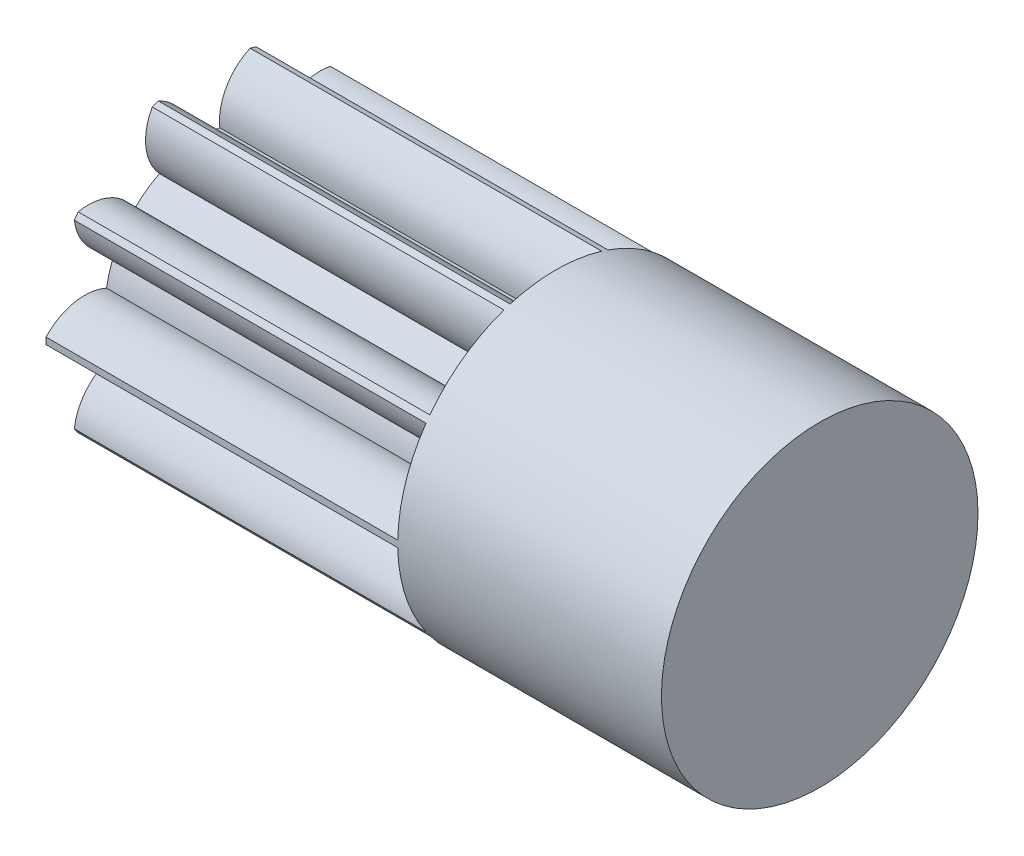
SolidWorks part; units mm, degrees
ref_plane "Plane1" through (0, 0, 0) normal (0, 0, 1) x (1, 0, 0)
ref_plane "Plane2" through (0, 0, 0) normal (0, 1, 0) x (1, 0, 0)
ref_plane "Plane3" through (0, 0, 0) normal (1, 0, 0) x (0, 0, -1)
sketch "HoldingSke" plane through (0, 0, 0) normal (0, 1, 0) x (1, 0, 0)
  line L0 (0, 0) -> (0.6565, -0.1158)
  line L1 (-15, 0) -> (100, 0) construction
  line L2 (0, 0) -> (-2.1039, 2.3779)
  line L3 (0, 0) -> (-11.863, 4.5341)
  line L4 (0, 0) -> (8.5048, 1.4996)
  line L5 (0, 0) -> (-46.8476, -17.4728)
  line L6 (0, 0) -> (-16.5793, -11.1861)
  line L7 (-2.1039, 2.3779) -> (8.6586, 51.2059)
  line L8 (-76.2, 54.61) -> (-75.3, 54.61)
  line L9 (-71.009, 38.7566) -> (-53.1078, 45.2721)
  line L10 (-76.2, 71.12) -> (104.1128, 71.12)
  line L11 (0, 0) -> (-20, 0)
  line L12 (-76.2, 101.6) -> (-76.147, 101.6)
  line L13 (24.9733, 27.94) -> (52.9518, 28.4284)
  line L14 (24.9733, 27.94) -> (24.9743, 27.94)
  line L15 (24.9733, 27.94) -> (100.4006, 29.5858)
  line L16 (-63.627, -1.5) -> (-12.827, -1.5)
  circle A0 centre (0, 0) radius 2.5
  circle A1 centre (0, 0) radius 5.624
  circle A2 centre (0, 0) radius 37.5
  circle A3 centre (0, 0) radius 2.5
  dimension "MHD" = 11.248
  dimension "Hub_dia" = 75
  dimension "Bore" = 5
  dimension "MBD" = 5
  dimension "Num_teeth" = 10
  dimension "Pitch" = 0.6667
  dimension "Overall_len" = 50
  dimension "Show_teeth" = 10
  dimension "Thickness" = 20
  dimension "OAL" = 50.0001
  dimension "T_dim" = 0.9
  dimension "Ap" = 20
  dimension "H" = 19.05
  dimension "Pitch_radius" = 180.3128
  dimension "Width" = 20
  dimension "Backlash" = 0.053
  dimension "Addendum_fac" = 1
  dimension "Dedendum_fac" = 1.25
  dimension "Clearance_fac" = 0.25
  dimension "Dedendum_add" = 0.001
  dimension "Module" = 1.5
sketch "BasProSke" plane through (0, 0, 0) normal (0, 1, 0) x (1, 0, 0)
  line L0 (-10, 0) -> (60, 0) construction
  line L1 (0, 0) -> (0, 9)
  line L2 (0, 0) -> (20, 0)
  line L3 (20, 0) -> (20, 9)
  line L4 (20, 9) -> (0, 9)
  dimension "Thickness" = 20
  dimension "Diameter" = 18
revolve "Base-Revolve" add sketch "BasProSke" angle 360 about L0
sketch "TooCutSke" plane through (0, 0, 0) normal (1, 0, 0) x (0, 0, -1)
  line L1 (0, 0) -> (0, 107) construction
  line L2 (0, 0) -> (-1.2658, 7.3924) construction
  line L3 (0, 0) -> (-4.5869, 14.117) construction
  line L4 (-1.2658, 7.3924) -> (-2.2934, 7.0585) construction
  arc A0 (0.8839, 5.5541) -> (-0.8839, 5.5541) centre (0, 0) ccw
  arc A1 (2.6378, 8.6313) -> (-2.6378, 8.6313) centre (0, 0) ccw
  circle A2 centre (0, 0) radius 7.5 construction
  circle A3 centre (0, 0) radius 7.0477 construction
  arc A4 (-0.8839, 5.5541) -> (-2.6378, 8.6313) centre (-3.8646, 5.8936) ccw
  arc A5 (2.6378, 8.6313) -> (0.8839, 5.5541) centre (3.8646, 5.8936) ccw
  dimension "Root_dia" = 11.248
  dimension "Overcut_dia" = 18.0508
  dimension "Pitch_dia" = 15
  dimension "Base_dia" = 14.0954
  dimension "Flank_rad" = 3
  dimension "Half_ang" = 18
  dimension "Half_CT" = 1.0805
extrude "ToothCut" cut sketch "TooCutSke" along normal through all
fillet "Breaks" [suppressed] radius 0.03
fillet "RootFillets" [suppressed] radius 0.376
pattern_circular "TeethCuts" count 10 every 36 about axis through (-10, 0, 0) along (1, 0, 0) of "ToothCut", "RootFillets", "Breaks"
sketch "HubNeaOneSke" plane through (0, 0, 0) normal (-1, 0, 0) x (0, 0, 1)
  circle A0 centre (0, 0) radius 5.624
  dimension "Diameter" = 11.248
extrude "HubNearOne" [suppressed] add sketch "HubNeaOneSke" along normal blind 30.0001
sketch "HubNeaBotSke" plane through (0, 0, 0) normal (-1, 0, 0) x (0, 0, 1)
  circle A0 centre (0, 0) radius 5.624
  dimension "Diameter" = 11.248
extrude "HubNearBoth" [suppressed] add sketch "HubNeaBotSke" along normal blind 15
ref_plane "FarPln" through (20, 0, 0) normal (1, 0, 0) x (0, 0, -1)
sketch "HubFarSke" plane through (20, 0, 0) normal (1, 0, 0) x (0, 0, -1)
  circle A0 centre (0, 0) radius 5.624
  dimension "Diameter" = 11.248
extrude "HubFar" [suppressed] add sketch "HubFarSke" along normal blind 15
sketch "BorSke" plane through (0, 0, 0) normal (1, 0, 0) x (0, 0, -1)
  circle A0 centre (0, 0) radius 2.5
  dimension "Diameter" = 5
extrude "Bore" cut sketch "BorSke" along normal mid plane 100.0001
sketch "KeySke" plane through (0, 0, 0) normal (1, 0, 0) x (0, 0, -1)
  line L0 (-1, 0) -> (-1, 3.4)
  line L1 (-1, 3.4) -> (1, 3.4)
  line L2 (1, 3.4) -> (1, 0)
  line L3 (0, 0) -> (0, 34) construction
  line L4 (-1, 0) -> (1, 0)
  dimension "Offset" = 3.4
extrude "Keyway" [suppressed] cut sketch "KeySke" along normal mid plane 100.0001
pattern_circular "Keyway2" [suppressed] count 2 every 90 about axis through (-10, 0, 0) along (1, 0, 0)
sketch "Çizim1" plane through (20, 0, 0) normal (1, 0, 0) x (0, 0, -1)
  circle A1 centre (0, 0) radius 3
  dimension "D1" = 6
extrude "Yükseklik-Ekstrüzyon3" add sketch "Çizim1" against normal blind 20
sketch "Çizim2" plane through (20, 0, 0) normal (1, 0, 0) x (0, 0, -1)
  circle A0 centre (0, 0) radius 9
extrude "Yükseklik-Ekstrüzyon4" add sketch "Çizim2" along normal blind 15
equation "' \"Module@HoldingSke\" = 6.35"
equation "' \"Num_teeth@HoldingSke\" = 12"
equation "' \"Ap@HoldingSke\" =  20"
equation "' \"Ap@HoldingSke\" = 20"
equation "' \"Width@HoldingSke\" = 0.5 * 25.4"
equation "' \"Hub_dia@HoldingSke\"= 1 * 25.4"
equation "' \"Hub_dia@HoldingSke\" = 1 * 25.4"
equation "' \"Overall_len@HoldingSke\" = 1.0 * 25.4"
equation "' \"Bore@HoldingSke\" = 0.75 * 25.4"
equation "' \"T_dim@HoldingSke\" = 0.1 * 25.4"
equation "' \"Width@KeySke\" = 0.25 * 25.4"
equation "' \"Show_teeth@HoldingSke\" = 13"
equation "' \"Backlash@HoldingSke\" = 0.009 * 25.4"
equation "' \"Addendum_fac@HoldingSke\" = 1.0"
equation "' \"Dedendum_fac@HoldingSke\" = 1.25"
equation "' \"Dedendum_add@HoldingSke\" = 0.00005 * 25.4"
equation "' \"Clearance_fac@HoldingSke\" = 0.25"
equation "\"Pitch@HoldingSke\" = 1 / \"Module@HoldingSke\""
equation "\"Overcut_dia@TooCutSke\" = (\"Num_teeth@HoldingSke\" + 2 * \"Addendum_fac@HoldingSke\") / \"Pitch@HoldingSke\" + 0.002 * 25.4"
equation "\"Pitch_dia@TooCutSke\" = \"Num_teeth@HoldingSke\" / \"Pitch@HoldingSke\""
equation "\"Base_dia@TooCutSke\" = \"Num_teeth@HoldingSke\" / \"Pitch@HoldingSke\" * cos((\"Ap@HoldingSke\"  * 3.14159265 / 180))"
equation "\"Root_dia@TooCutSke\" = (\"Num_teeth@HoldingSke\" + 2) / \"Pitch@HoldingSke\" - 2 * (\"Addendum_fac@HoldingSke\" + \"Dedendum_fac@HoldingSke\") / \"Pitch@HoldingSke\" - \"Dedendum_add@HoldingSke\" * 2"
equation "\"Half_ang@TooCutSke\" = 180 / \"Num_teeth@HoldingSke\""
equation "\"Half_CT@TooCutSke\" = \"Num_teeth@HoldingSke\" / \"Pitch@HoldingSke\" * sin((3.14159265 / 2 / \"Num_teeth@HoldingSke\")) / 2 - 7 * \"Backlash@HoldingSke\" / 4"
equation "\"Flank_rad@TooCutSke\" = \"Num_teeth@HoldingSke\" / \"Pitch@HoldingSke\" / 5"
equation "\"Radius@RootFillets\" = \"Clearance_fac@HoldingSke\" / \"Pitch@HoldingSke\" + \"Dedendum_add@HoldingSke\""
equation "\"Break_rad@Breaks\" = 0.02 / \"Pitch@HoldingSke\""
equation "\"Thickness@HoldingSke\" = \"Width@HoldingSke\""
equation "\"OAL@HoldingSke\" = \"Thickness@HoldingSke\""
equation "\"MHD@HoldingSke\" = (\"Num_teeth@HoldingSke\" + 2) / \"Pitch@HoldingSke\" - 2 * (\"Addendum_fac@HoldingSke\" + \"Dedendum_fac@HoldingSke\")  / \"Pitch@HoldingSke\" - \"Dedendum_add@HoldingSke\" * 2"
equation "\"MBD@HoldingSke\" = (\"Num_teeth@HoldingSke\" + 2) / \"Pitch@HoldingSke\" - 2 * (\"Addendum_fac@HoldingSke\" + \"Dedendum_fac@HoldingSke\")  / \"Pitch@HoldingSke\" - \"Dedendum_add@HoldingSke\" * 2 - 0.002 * 25.4"
equation "\"MHD@HoldingSke\" = ((sgn( \"MHD@HoldingSke\" - \"Hub_dia@HoldingSke\" )-1)*( \"MHD@HoldingSke\" - \"Hub_dia@HoldingSke\" ))/-2+ \"Hub_dia@HoldingSke\""
equation "\"MBD@HoldingSke\" = ((sgn( \"MBD@HoldingSke\" - \"Bore@HoldingSke\" )-1)*( \"MBD@HoldingSke\" - \"Bore@HoldingSke\" ))/-2+ \"Bore@HoldingSke\""
equation "\"OAL@HoldingSke\" = ((sgn( \"OAL@HoldingSke\" - \"Overall_len@HoldingSke\" )+1)*( \"OAL@HoldingSke\" - \"Overall_len@HoldingSke\" ))/2 + \"Overall_len@HoldingSke\" + 0.000002 * 25.4"
equation "\"Num_teeth@TeethCuts\" = int( \"Show_teeth@HoldingSke\" ) + 1"
equation "\"Num_teeth@TeethCuts\" = ((sgn( \"Num_teeth@TeethCuts\" - \"Num_teeth@HoldingSke\" )-1)*( \"Num_teeth@TeethCuts\" - \"Num_teeth@HoldingSke\" ))/-2+ \"Num_teeth@HoldingSke\""
equation "\"Num_teeth@TeethCuts\" = ((sgn( \"Num_teeth@TeethCuts\" - 2.0)+1)*( \"Num_teeth@TeethCuts\" - 2.0))/2 +2.0"
equation "\"Angle@TeethCuts\" = 360.0 / \"Num_teeth@HoldingSke\""
equation "\"Diameter@BasProSke\" = (\"Num_teeth@HoldingSke\" + 2 * \"Addendum_fac@HoldingSke\") / \"Pitch@HoldingSke\""
equation "\"Thickness@BasProSke\"  = \"Thickness@HoldingSke\""
equation "' \"Fillet_rad@BasProSke\" =  \"Thickness@HoldingSke\" * 0.05"
equation "' \"Fillet_rad@BasProSke\" = \"Thickness@HoldingSke\" * 0.05"
equation "\"MHD@HoldingSke\" = ((sgn( \"MHD@HoldingSke\" - \"Root_dia@TooCutSke\" )-1)*( \"MHD@HoldingSke\" - \"Root_dia@TooCutSke\" ))/-2+ \"Root_dia@TooCutSke\""
equation "\"Diameter@HubNeaOneSke\" = \"MHD@HoldingSke\""
equation "\"Length@HubNearOne\" = \"OAL@HoldingSke\" - \"Thickness@BasProSke\""
equation "\"Diameter@HubNeaBotSke\" = \"MHD@HoldingSke\""
equation "\"Length@HubNearBoth\" = ( \"OAL@HoldingSke\" - \"Thickness@BasProSke\" ) / 2.0"
equation "\"Thickness@FarPln\" = \"Thickness@BasProSke\""
equation "\"Diameter@HubFarSke\" = \"MHD@HoldingSke\""
equation "\"Length@HubFar\" = ( \"OAL@HoldingSke\" - \"Thickness@BasProSke\" ) / 2.0"
equation "\"Diameter@BorSke\" = \"MBD@HoldingSke\""
equation "\"D1@Bore\" = \"OAL@HoldingSke\" * 2.0"
equation "\"D1@Keyway\" = \"OAL@HoldingSke\" * 2.0"
equation "\"Offset@KeySke\" = \"T_dim@HoldingSke\" + \"MBD@HoldingSke\" / 2.0"
